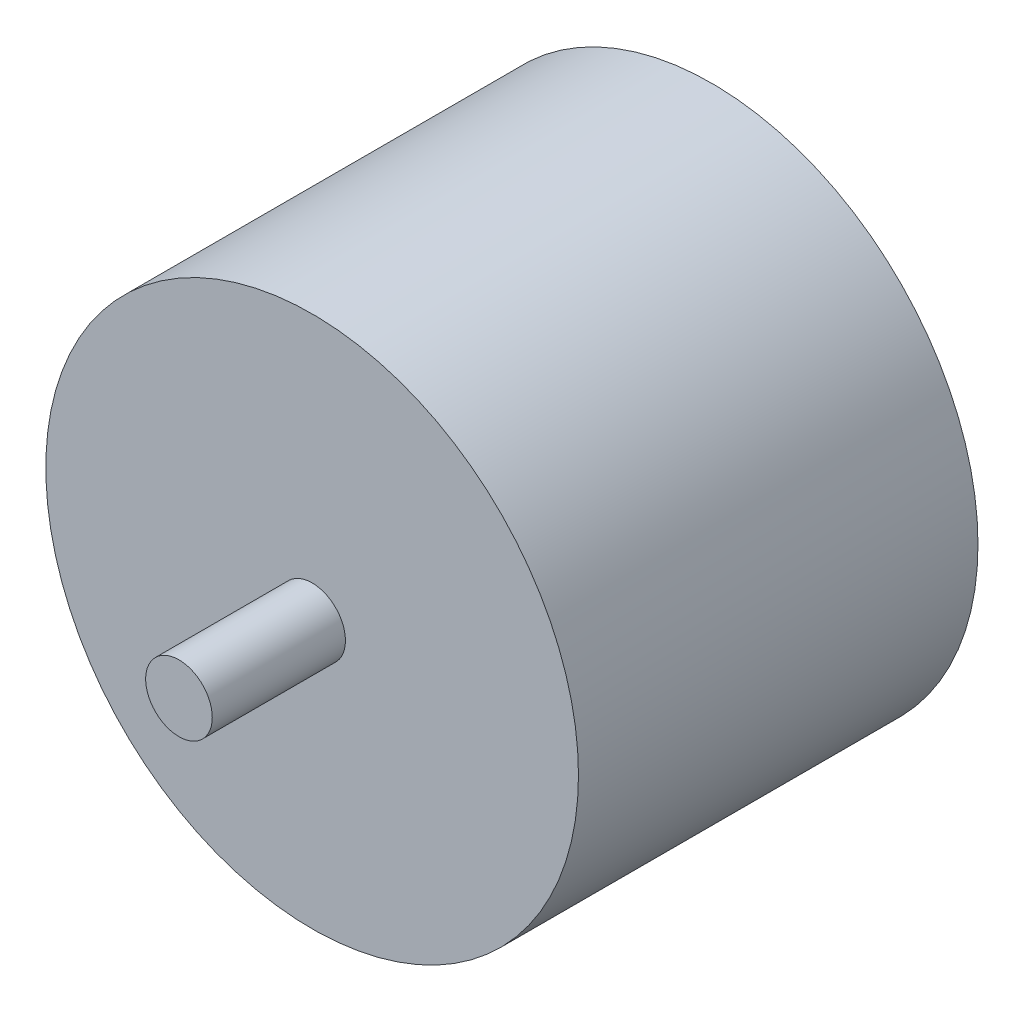
SolidWorks part; units mm, degrees
ref_plane "Front Plane" through (0, 0, 0) normal (0, 0, 1) x (1, 0, 0)
ref_plane "Top Plane" through (0, 0, 0) normal (0, 1, 0) x (1, 0, 0)
ref_plane "Right Plane" through (0, 0, 0) normal (1, 0, 0) x (0, 0, -1)
sketch "Sketch1" plane through (0, 0, 0) normal (0, 0, 1) x (1, 0, 0)
  circle A0 centre (0, 0) radius 25.4
  dimension "D1" = 50.8
extrude "Boss-Extrude1" add sketch "Sketch1" along normal mid plane 38.1
sketch "Sketch2" plane through (0, 0, 19.05) normal (0, 0, 1) x (1, 0, 0)
  circle A0 centre (0, 0) radius 3.175
  dimension "D1" = 6.35
extrude "Boss-Extrude2" add sketch "Sketch2" along normal blind 12.7
mirror "Mirror1" about plane through (0, 0, 0) normal (0, 0, 1) of "Boss-Extrude2"
